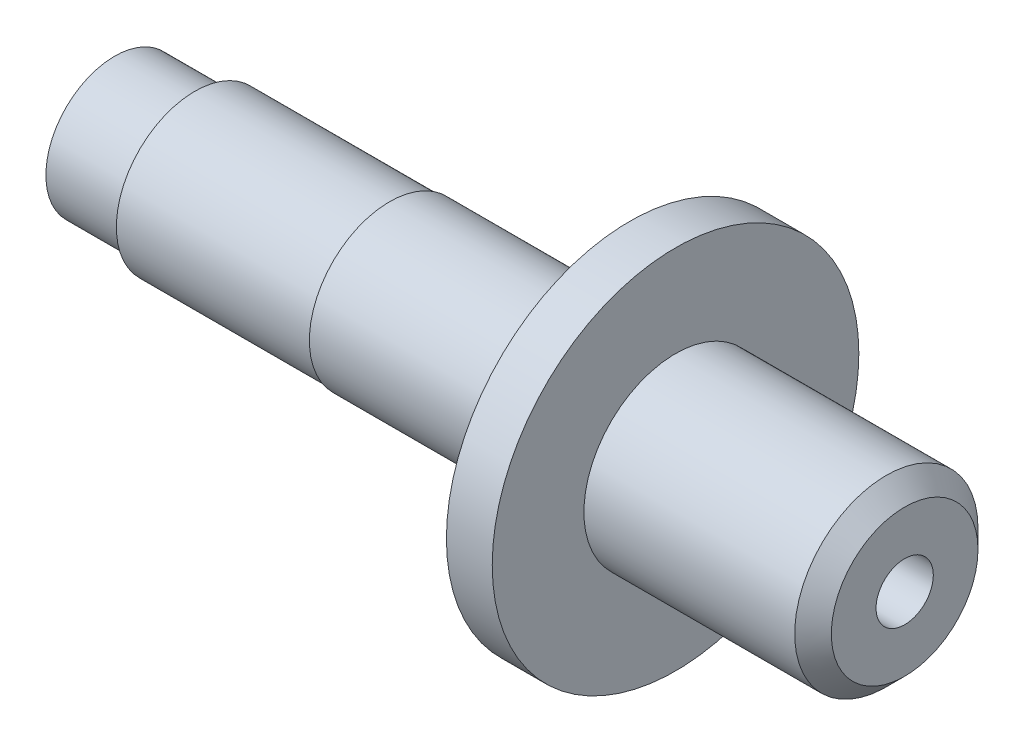
SolidWorks part; units mm, degrees
material "Titanium"
ref_plane "Front Plane" through (0, 0, 0) normal (0, 0, 1) x (1, 0, 0)
ref_plane "Top Plane" through (0, 0, 0) normal (0, 1, 0) x (1, 0, 0)
ref_plane "Right Plane" through (0, 0, 0) normal (1, 0, 0) x (0, 0, -1)
sketch3d "3DSketch4"
  line L0 (0, 0, 0) -> (0, 9.525, 0)
  line L1 (0, 9.525, 0) -> (11.1125, 9.525, 0)
  line L2 (11.1125, 9.525, 0) -> (11.1125, 10.8779, 0)
  line L3 (11.1125, 10.8779, 0) -> (38.1, 10.8779, 0)
  line L4 (38.1, 10.8779, 0) -> (38.1, 11.1192, 0)
  line L5 (38.1, 11.1192, 0) -> (65.024, 11.1192, 0)
  line L6 (65.024, 11.1192, 0) -> (65.024, 12.7114, 0)
  line L7 (65.024, 12.7114, 0) -> (66.294, 12.7114, 0)
  line L8 (71.374, 17.7914, 0) -> (71.374, 25.4125, 0)
  line L9 (71.374, 25.4125, 0) -> (77.724, 25.4125, 0)
  line L10 (77.724, 25.4125, 0) -> (77.724, 12.7136, 0)
  line L11 (77.724, 12.7136, 0) -> (109.474, 12.7136, 0)
  line L12 (109.474, 12.7136, 0) -> (109.474, 0.0192, 0)
  line L13 (0, 0, 0) -> (109.474, 0.0192, 0)
  arc A0 (66.294, 12.7114, 0) -> (71.374, 17.7914, 0) centre (66.294, 17.7914, 0) ccw
  point P17 (71.374, 12.7114, 0)
  point P18 (66.294, 17.7914, 5.08)
  dimension "D13" = 5.08
  dimension "D1" = 9.525
  dimension "D5" = 11.1125
  dimension "D2" = 11.1125
  dimension "D3" = 38.1
  dimension "D4" = 10.8712
  dimension "D9" = 65.024
  dimension "D6" = 12.7
  dimension "D7" = 25.4
  dimension "D8" = 12.7
  dimension "D10" = 31.75
  dimension "D11" = 6.35
  dimension "D12" = 109.474
sketch "Sketch4" plane through (0, 0, 0) normal (0, 0, 1) x (1, 0, 0)
  line L0 (0, 0) -> (0, 9.525)
  line L1 (0, 9.525) -> (11.1125, 9.525)
  line L2 (11.1125, 9.525) -> (11.1125, 10.8712)
  line L3 (11.1125, 10.8712) -> (38.1, 10.8712)
  line L4 (38.1, 10.8712) -> (38.1, 11.1125)
  line L5 (38.1, 11.1125) -> (65.024, 11.1125)
  line L6 (65.024, 11.1125) -> (65.024, 12.7)
  line L7 (65.024, 12.7) -> (66.294, 12.7)
  line L8 (71.374, 17.78) -> (71.374, 25.4)
  line L9 (71.374, 25.4) -> (77.724, 25.4)
  line L10 (77.724, 25.4) -> (77.724, 12.7)
  line L11 (77.724, 12.7) -> (109.474, 12.7)
  line L12 (109.474, 12.7) -> (109.474, 0)
  line L13 (109.474, 0) -> (0, 0)
  arc A0 (66.294, 12.7) -> (71.374, 17.78) centre (66.294, 17.78) ccw
  point P17 (71.374, 12.7)
  dimension "D15" = 5.08
  dimension "D1" = 9.525
  dimension "D2" = 10.8712
  dimension "D3" = 11.1125
  dimension "D4" = 12.7
  dimension "D5" = 25.4
  dimension "D6" = 12.7
  dimension "D7" = 11.1125
  dimension "D8" = 38.1
  dimension "D9" = 65.024
  dimension "D10" = 12.7
  dimension "D11" = 31.75
  dimension "D12" = 6.35
  dimension "D13" = 109.474
  dimension "D14" = 6.35
revolve "Revolve2" add sketch "Sketch4" angle 360 about L13
sketch "Sketch5" plane through (0, 0, 0) normal (-1, 0, 0) x (0, 0, 1)
  circle A0 centre (0, 0) radius 3.9688
  dimension "D1" = 7.9375
extrude "Cut-Extrude1" cut sketch "Sketch5" against normal blind 28.575
sketch "Sketch6" plane through (109.474, 0, 0) normal (1, 0, 0) x (0, 0, -1)
  circle A0 centre (0, 0) radius 3.9688
  dimension "D1" = 7.9375
extrude "Cut-Extrude2" cut sketch "Sketch6" against normal blind 33.782
chamfer "Chamfer1" distance 2.54 angle 45 1 edges at (109.474, 0, -12.7)
